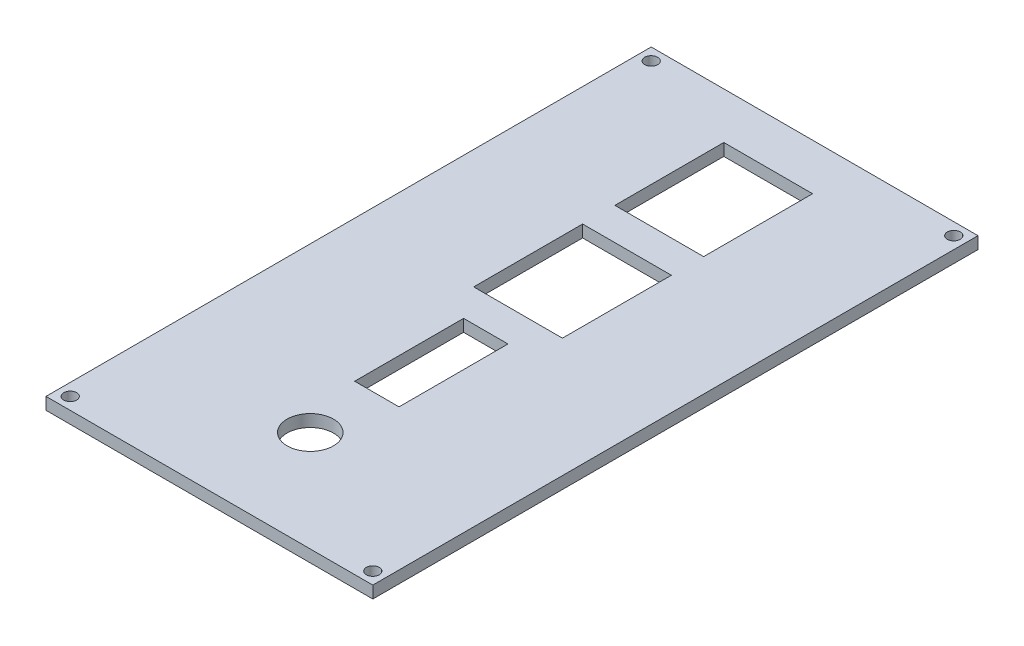
SolidWorks part; units mm, degrees
ref_plane "Front Plane" through (0, 0, 0) normal (0, 0, 1) x (1, 0, 0)
ref_plane "Top Plane" through (0, 0, 0) normal (0, 1, 0) x (1, 0, 0)
ref_plane "Right Plane" through (0, 0, 0) normal (1, 0, 0) x (0, 0, -1)
sketch "Sketch1" plane through (0, 0, 0) normal (0, 1, 0) x (1, 0, 0)
  line L1 (0, 0) -> (81, 0)
  line L2 (0, 0) -> (0, 150)
  line L3 (0, 150) -> (81, 150)
  line L4 (81, 0) -> (81, 150)
  dimension "D1" = 81
  dimension "D2" = 150
extrude "Boss-Extrude1" add sketch "Sketch1" along normal blind 3
sketch "Sketch2" plane through (0, 3, 0) normal (0, 1, 0) x (1, 0, 0)
  line L1 (0, 0) -> (3, 0)
  line L2 (0, 0) -> (0, 3)
  line L3 (0, 3) -> (3, 3)
  line L4 (3, 0) -> (3, 3)
  line L5 (0, 150) -> (3, 150)
  line L6 (0, 150) -> (0, 147)
  line L7 (0, 147) -> (3, 147)
  line L8 (3, 150) -> (3, 147)
  line L9 (81, 150) -> (78, 150)
  line L10 (81, 150) -> (81, 147)
  line L11 (81, 147) -> (78, 147)
  line L12 (78, 150) -> (78, 147)
  line L13 (81, 0) -> (78, 0)
  line L14 (81, 0) -> (81, 3)
  line L15 (81, 3) -> (78, 3)
  line L16 (78, 0) -> (78, 3)
  dimension "D1" = 3
  dimension "D2" = 3
  dimension "D3" = 3
  dimension "D4" = 3
  dimension "D5" = 3
  dimension "D6" = 3
  dimension "D7" = 3
  dimension "D8" = 3
hole_wizard "M3 Clearance Hole1" positions "3DSketch1" profile "Sketch4" hole size "M3" standard "ANSI Metric" end condition through all
sketch3d "3DSketch1"
  point P0 (3, 3, -147)
  point P3 (78, 3, -147)
  point P6 (78, 3, -3)
  point P9 (3, 3, -3)
sketch "Sketch4" plane through (3, 3, -147) normal (1, 0, 0) x (0, 0, 1)
  line L0 (0, 0) -> (0, 3)
  line L1 (0, 3) -> (1.6, 3)
  line L2 (1.6, 3) -> (1.6, 0)
  line L5 (1.6, 0) -> (0, 0)
  line L11 (0, -6.35) -> (0, 107.95) construction
  dimension "Thru Hole Dia." = 3.2
  dimension "Thru Hole Depth" = 3
sketch "Sketch8" plane through (0, 0, -150) normal (0, 0, -1) x (-1, 0, 0)
  line L0 (0, 3) -> (0, 0)
sketch "Sketch9" plane through (0, 3, 0) normal (0, 1, 0) x (1, 0, 0)
  line L0 (0, 125) -> (81, 125) construction
  line L1 (0, 150) -> (0, 0) construction
  line L2 (81, 0) -> (81, 150) construction
  line L3 (0, 90) -> (81, 90) construction
  line L4 (0, 55) -> (81, 55) construction
  line L5 (0, 25) -> (81, 25) construction
  line L6 (81, 150) -> (0, 150) construction
  line L7 (0, 0) -> (81, 0) construction
  line L9 (29.5, 138.5) -> (51.5, 138.5)
  line L10 (29.5, 138.5) -> (29.5, 111.5)
  line L11 (29.5, 111.5) -> (51.5, 111.5)
  line L12 (51.5, 138.5) -> (51.5, 111.5)
  line L13 (29.5, 138.5) -> (51.5, 111.5) construction
  line L14 (29.5, 111.5) -> (51.5, 138.5) construction
  line L15 (29.5, 103.5) -> (51.5, 103.5)
  line L16 (29.5, 103.5) -> (29.5, 76.5)
  line L17 (29.5, 76.5) -> (51.5, 76.5)
  line L18 (51.5, 103.5) -> (51.5, 76.5)
  line L19 (29.5, 103.5) -> (51.5, 76.5) construction
  line L20 (29.5, 76.5) -> (51.5, 103.5) construction
  line L21 (35, 68.5) -> (46, 68.5)
  line L22 (35, 68.5) -> (35, 41.5)
  line L23 (35, 41.5) -> (46, 41.5)
  line L24 (46, 68.5) -> (46, 41.5)
  line L25 (35, 68.5) -> (46, 41.5) construction
  line L26 (35, 41.5) -> (46, 68.5) construction
  circle A0 centre (40.5, 25) radius 5.75
  point P16 (40.5, 125)
  point P21 (40.5, 90)
  point P26 (40.5, 55)
  dimension "D6" = 11.5
  dimension "D1" = 25
  dimension "D2" = 35
  dimension "D3" = 35
  dimension "D4" = 30
  dimension "D5" = 25
  dimension "D7" = 27
  dimension "D8" = 22
  dimension "D9" = 27
  dimension "D10" = 22
  dimension "D11" = 27
  dimension "D12" = 11
extrude "Cut-Extrude1" cut sketch "Sketch9" against normal through all
